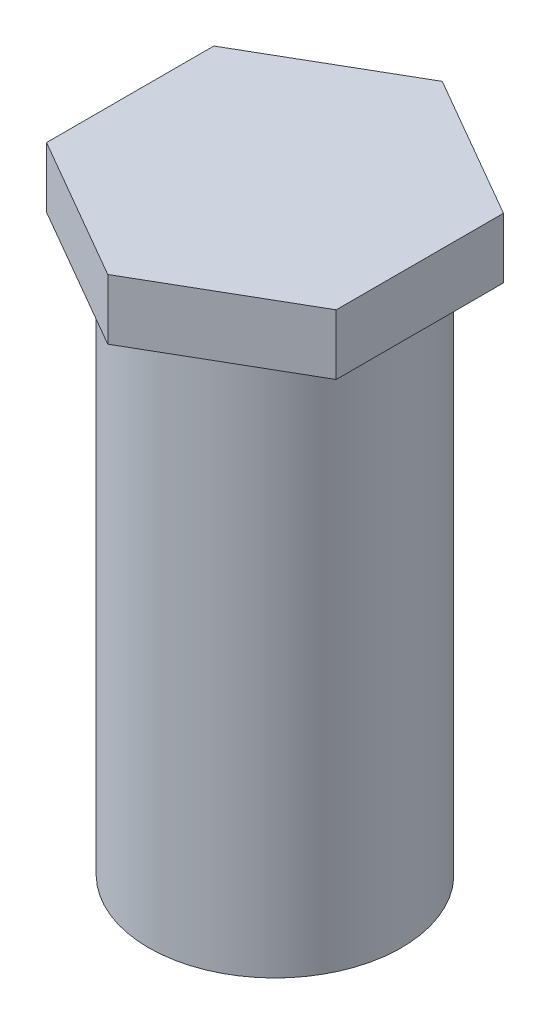
SolidWorks part; units mm, degrees
material "acero"
ref_plane "Alzado" through (0, 0, 0) normal (0, 0, 1) x (1, 0, 0)
ref_plane "Planta" through (0, 0, 0) normal (0, 1, 0) x (1, 0, 0)
ref_plane "Vista lateral" through (0, 0, 0) normal (1, 0, 0) x (0, 0, -1)
sketch "Croquis1" plane through (0, 0, 0) normal (0, 0, 1) x (1, 0, 0)
  line L0 (0, 0) -> (0, -60.9498) construction
  line L1 (0, 0) -> (2.095, 0)
  line L4 (2.095, 0) -> (2.095, -10)
  line L5 (2.095, -10) -> (0, -10)
  line L6 (0, -10) -> (0, 0)
  dimension "D1" = 10
  dimension "D4" = 4.19
revolve "Revolución1" add sketch "Croquis1" angle 360 about L0
sketch "Croquis2" plane through (0, 0, 0) normal (0, 1, 0) x (1, 0, 0)
  line L1 (2.4, -1.3856) -> (2.4, 1.3856)
  line L2 (2.4, 1.3856) -> (0, 2.7713)
  line L3 (0, 2.7713) -> (-2.4, 1.3856)
  line L4 (-2.4, 1.3856) -> (-2.4, -1.3856)
  line L5 (-2.4, -1.3856) -> (0, -2.7713)
  line L6 (0, -2.7713) -> (2.4, -1.3856)
  circle A0 centre (0, 0) radius 2.4 construction
  dimension "D1" = 4.8
extrude "Saliente-Extruir1" add sketch "Croquis2" against normal blind 1
hole_wizard "Taladro roscado M31" positions "Croquis4" profile "Croquis3" tap size "M3" standard "Din"
sketch "Croquis4" plane through (0, -10, 0) normal (0, -1, 0) x (-1, 0, 0)
  point P0 (0, 0)
sketch "Croquis3" plane through (0, -10, 0) normal (1, 0, 0) x (0, 0, -1)
  line L0 (0, 0) -> (0, 4.7511)
  line L1 (0, 4.7511) -> (1.25, 4)
  line L2 (1.25, 4) -> (1.25, 0)
  line L5 (1.25, 0) -> (0, 0)
  line L10 (0, 4.7511) -> (-1.25, 4) construction
  line L11 (0, -6.35) -> (0, 107.95) construction
  dimension "Diámetro de perforador para roscar" = 2.5
  dimension "Profundidad de perforador para roscar" = 4
  dimension "Ángulo de perforador" = 118
cosmetic thread "Rosca de taladro1" parameters "D1"=4, "D2"=3
